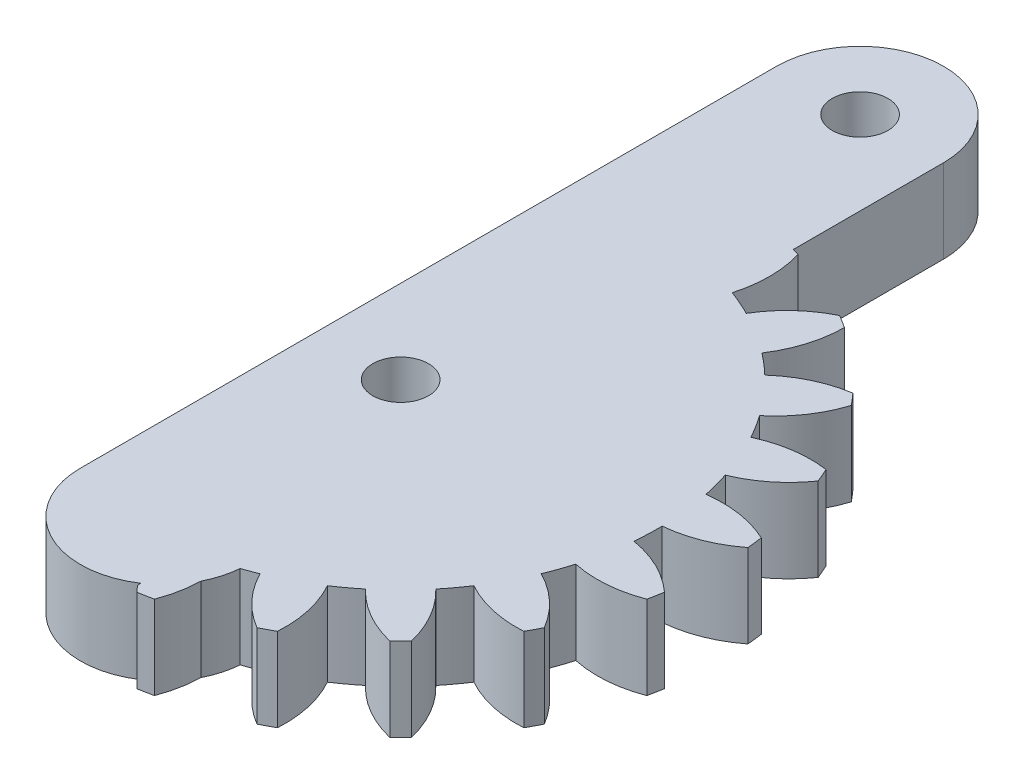
SolidWorks part; units mm, degrees
material "Acrylic (Medium-high impact)"
ref_plane "Front Plane" through (0, 0, 0) normal (0, 0, 1) x (1, 0, 0)
ref_plane "Top Plane" through (0, 0, 0) normal (0, 1, 0) x (1, 0, 0)
ref_plane "Right Plane" through (0, 0, 0) normal (1, 0, 0) x (0, 0, -1)
sketch "Sketch1" plane through (0, 0, 0) normal (0, 1, 0) x (1, 0, 0)
  line L1 (6, -17) -> (6, 33)
  line L2 (-6, -17) -> (-5.9999, 33)
  arc A0 (6, -17) -> (-6, -17) centre (0, -17) cw
  arc A1 (-5.9999, 33) -> (6, 33) centre (0, 33) cw
  dimension "D1" = 50
  dimension "D3" = 50
extrude "Boss-Extrude1" add sketch "Sketch1" along normal blind 6
sketch "Sketch4" plane through (0, 6, 0) normal (0, 1, 0) x (1, 0, 0)
  line L0 (-2.743, 18.1997) -> (3.3513, -22.2356)
  arc A1 (12.6946, 19.1793) -> (11.7723, 19.7589) centre (0, 0) ccw
  arc A2 (11.3096, 14.6392) -> (12.6946, 19.1793) centre (4.295, 19.2605) ccw
  arc A3 (12.7903, 13.3649) -> (11.3096, 14.6392) centre (0, 0) ccw
  arc A4 (17.0733, 15.4111) -> (12.7903, 13.3649) centre (18.4053, 7.1174) ccw
  arc A5 (17.7838, 14.5854) -> (17.0733, 15.4111) centre (0, 0) ccw
  arc A6 (15.1221, 10.6553) -> (17.7838, 14.5854) centre (9.7813, 17.1388) ccw
  arc A7 (16.1614, 9.0011) -> (15.1221, 10.6553) centre (0, 0) ccw
  arc A8 (20.8573, 9.694) -> (16.1614, 9.0011) centre (19.6855, 1.3761) ccw
  arc A9 (21.2929, 8.6956) -> (20.8573, 9.694) centre (0, 0) ccw
  arc A10 (17.591, 5.7246) -> (21.2929, 8.6956) centre (14.3985, 13.4943) ccw
  arc A11 (18.0966, 3.8376) -> (17.591, 5.7246) centre (0, 0) ccw
  arc A12 (22.788, 3.1155) -> (18.0966, 3.8376) centre (19.2166, -4.4874) ccw
  arc A13 (22.91, 2.0331) -> (22.788, 3.1155) centre (0, 0) ccw
  arc A14 (18.4968, 0.2852) -> (22.91, 2.0331) centre (17.7363, 8.6507) ccw
  arc A15 (18.4237, -1.667) -> (18.4968, 0.2852) centre (0, 0) ccw
  arc A16 (22.6939, -3.7398) -> (18.4237, -1.667) centre (17.0401, -9.9522) ccw
  arc A17 (22.4914, -4.8101) -> (22.6939, -3.7398) centre (0, 0) ccw
  arc A18 (17.7591, -5.1795) -> (22.4914, -4.8101) centre (19.4982, 3.0385) ccw
  arc A19 (17.1139, -7.0234) -> (17.7591, -5.1795) centre (0, 0) ccw
  arc A20 (20.5834, -10.2628) -> (17.1139, -7.0234) centre (13.3496, -14.5327) ccw
  arc A21 (20.0744, -11.2259) -> (20.5834, -10.2628) centre (0, 0) ccw
  arc A22 (15.4434, -10.184) -> (20.0744, -11.2259) centre (19.5276, -2.8437) ccw
  arc A23 (14.2834, -11.7558) -> (15.4434, -10.184) centre (0, 0) ccw
  arc A24 (16.6439, -15.8739) -> (14.2834, -11.7558) centre (8.4729, -17.822) ccw
  arc A25 (15.8736, -16.6441) -> (16.6439, -15.8739) centre (0, 0) ccw
  arc A26 (11.7556, -14.2835) -> (15.8736, -16.6441) centre (17.8218, -8.4732) ccw
  arc A27 (10.1837, -15.4436) -> (11.7556, -14.2835) centre (0, 0) ccw
  arc A28 (11.2256, -20.0745) -> (10.1837, -15.4436) centre (2.8434, -19.5276) ccw
  arc A29 (10.2625, -20.5835) -> (11.2256, -20.0745) centre (0, 0) ccw
  arc A30 (7.0231, -17.114) -> (10.2625, -20.5835) centre (14.5325, -13.3498) ccw
  arc A31 (5.1792, -17.7592) -> (7.0231, -17.114) centre (0, 0) ccw
  arc A32 (4.8098, -22.4915) -> (5.1792, -17.7592) centre (-3.0388, -19.4982) ccw
  arc A33 (3.7394, -22.694) -> (4.8098, -22.4915) centre (0, 0) ccw
  arc A34 (3.3513, -22.2356) -> (3.7394, -22.694) centre (9.952, -17.0403) ccw
  arc A79 (3.0173, 18.1563) -> (-2.743, 18.1997) centre (0, 0) ccw
  arc A80 (5.4252, 22.351) -> (3.0173, 18.1563) centre (11.1978, 16.2487) ccw
  arc A81 (6.4774, 22.069) -> (5.4252, 22.351) centre (0, 0) ccw
  arc A82 (6.4921, 17.3224) -> (6.4774, 22.069) centre (-1.5729, 19.6708) ccw
  arc A83 (8.2827, 16.5412) -> (6.4921, 17.3224) centre (0, 0) ccw
  arc A84 (11.7723, 19.7589) -> (8.2827, 16.5412) centre (15.4897, 12.2262) ccw
extrude "Boss-Extrude2" add sketch "Sketch4" against normal blind 6
sketch "Sketch2" plane through (0, 6, 0) normal (0, 1, 0) x (1, 0, 0)
  line L0 (-7.3626, 16.5) -> (11.1888, 16.5) construction
  circle A0 centre (0, 0) radius 2
  circle A1 centre (0, 33) radius 2
  dimension "D1" = 33
extrude "Cut-Extrude1" cut sketch "Sketch2" against normal through all
